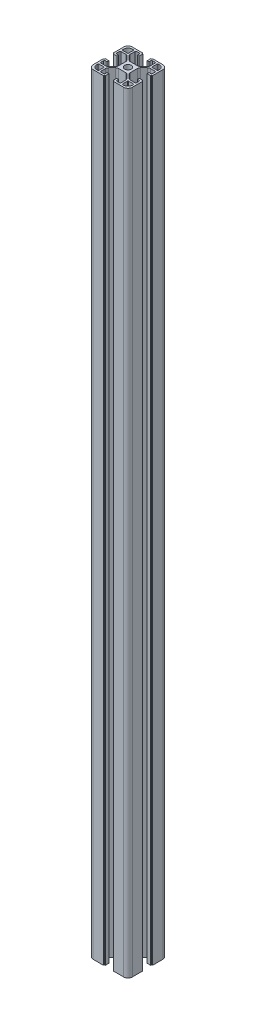
SolidWorks part; units mm, degrees
ref_plane "Front Plane" through (0, 0, 0) normal (0, 0, 1) x (1, 0, 0)
ref_plane "Top Plane" through (0, 0, 0) normal (0, 1, 0) x (1, 0, 0)
ref_plane "Right Plane" through (0, 0, 0) normal (1, 0, 0) x (0, 0, -1)
sketch "Sketch1" plane through (0, 0, 0) normal (0, 1, 0) x (1, 0, 0)
  line L0 (84.1702, 31.7204) -> (84.1702, 42.1204)
  line L1 (44.1702, 62.7204) -> (44.1702, 52.3204)
  line L2 (48.6702, 27.2204) -> (59.0702, 27.2204)
  line L3 (79.6702, 67.2204) -> (69.2702, 67.2204)
  line L4 (84.1702, 52.3204) -> (84.1702, 62.7204)
  line L6 (44.1702, 42.1204) -> (44.1702, 31.7204)
  line L7 (69.2702, 27.2204) -> (79.6702, 27.2204)
  line L10 (44.1702, 42.1204) -> (44.7702, 42.1204)
  line L11 (44.9702, 42.3204) -> (44.9702, 42.9204)
  line L12 (48.6702, 43.1204) -> (45.1702, 43.1204)
  line L13 (48.6702, 41.3204) -> (48.6702, 43.1204)
  line L14 (46.9702, 41.3204) -> (48.6702, 41.3204)
  line L15 (45.9702, 37.9704) -> (45.9702, 40.3204)
  line L16 (51.6169, 36.9704) -> (46.9702, 36.9704)
  line L17 (57.2915, 41.4024) -> (53.7382, 37.8491)
  line L18 (58.1702, 50.9171) -> (58.1702, 43.5237)
  line L19 (53.7382, 56.5917) -> (57.2915, 53.0384)
  line L20 (46.9702, 57.4704) -> (51.6169, 57.4704)
  line L21 (45.9702, 54.1204) -> (45.9702, 56.4704)
  line L22 (48.6702, 53.1204) -> (46.9702, 53.1204)
  line L23 (48.6702, 51.3204) -> (48.6702, 53.1204)
  line L24 (45.1702, 51.3204) -> (48.6702, 51.3204)
  line L25 (44.9702, 51.5204) -> (44.9702, 52.1204)
  line L26 (44.7702, 52.3204) -> (44.1702, 52.3204)
  line L28 (59.0702, 67.2204) -> (48.6702, 67.2204)
  line L29 (59.0702, 67.2204) -> (59.0702, 66.6204)
  line L30 (59.2702, 66.4204) -> (60.0702, 66.4204)
  line L31 (60.0702, 62.7204) -> (60.0702, 66.4204)
  line L32 (58.2702, 62.7204) -> (60.0702, 62.7204)
  line L33 (58.2702, 64.4204) -> (58.2702, 62.7204)
  line L34 (54.9202, 65.4204) -> (57.2702, 65.4204)
  line L35 (53.9202, 59.7737) -> (53.9202, 64.4204)
  line L36 (58.3522, 54.0991) -> (54.7989, 57.6524)
  line L37 (67.8669, 53.2204) -> (60.4735, 53.2204)
  line L38 (73.5415, 57.6524) -> (69.9882, 54.0991)
  line L39 (74.4202, 64.4204) -> (74.4202, 59.7737)
  line L40 (71.0702, 65.4204) -> (73.4202, 65.4204)
  line L41 (70.0702, 62.7204) -> (70.0702, 64.4204)
  line L42 (68.2702, 62.7204) -> (70.0702, 62.7204)
  line L43 (68.2702, 66.2204) -> (68.2702, 62.7204)
  line L44 (68.4702, 66.4204) -> (69.2702, 66.4204)
  line L45 (69.2702, 66.4204) -> (69.2702, 67.2204)
  line L48 (84.1702, 52.3204) -> (83.5702, 52.3204)
  line L49 (83.3702, 52.1204) -> (83.3702, 51.5204)
  line L50 (79.6702, 51.3204) -> (83.1702, 51.3204)
  line L51 (79.6702, 53.1204) -> (79.6702, 51.3204)
  line L52 (81.3702, 53.1204) -> (79.6702, 53.1204)
  line L53 (82.3702, 56.4704) -> (82.3702, 54.1204)
  line L54 (76.7235, 57.4704) -> (81.3702, 57.4704)
  line L55 (71.0489, 53.0384) -> (74.6022, 56.5917)
  line L56 (70.1702, 43.5237) -> (70.1702, 50.9171)
  line L57 (74.6022, 37.8491) -> (71.0489, 41.4024)
  line L58 (81.3702, 36.9704) -> (76.7235, 36.9704)
  line L59 (82.3702, 40.3204) -> (82.3702, 37.9704)
  line L60 (79.6702, 41.3204) -> (81.3702, 41.3204)
  line L61 (79.6702, 43.1204) -> (79.6702, 41.3204)
  line L62 (83.1702, 43.1204) -> (79.6702, 43.1204)
  line L63 (83.3702, 42.9204) -> (83.3702, 42.3204)
  line L64 (83.5702, 42.1204) -> (84.1702, 42.1204)
  line L67 (69.2702, 27.2204) -> (69.2702, 27.8204)
  line L68 (69.0702, 28.0204) -> (68.4702, 28.0204)
  line L69 (68.2702, 31.7204) -> (68.2702, 28.2204)
  line L70 (70.0702, 31.7204) -> (68.2702, 31.7204)
  line L71 (70.0702, 30.0204) -> (70.0702, 31.7204)
  line L72 (73.4202, 29.0204) -> (71.0702, 29.0204)
  line L73 (74.4202, 34.6671) -> (74.4202, 30.0204)
  line L74 (69.9882, 40.3417) -> (73.5415, 36.7884)
  line L75 (60.4735, 41.2204) -> (67.8669, 41.2204)
  line L76 (54.7989, 36.7884) -> (58.3522, 40.3417)
  line L77 (53.9202, 30.0204) -> (53.9202, 34.6671)
  line L78 (57.2702, 29.0204) -> (54.9202, 29.0204)
  line L79 (58.2702, 31.7204) -> (58.2702, 30.0204)
  line L80 (60.0702, 31.7204) -> (58.2702, 31.7204)
  line L81 (60.0702, 28.2204) -> (60.0702, 31.7204)
  line L82 (59.8702, 28.0204) -> (59.2702, 28.0204)
  line L83 (59.0702, 27.8204) -> (59.0702, 27.2204)
  line L84 (82.3702, 34.6704) -> (82.3702, 33.5204)
  line L85 (76.7202, 35.1704) -> (81.8702, 35.1704)
  line L86 (76.2202, 29.5204) -> (76.2202, 34.6704)
  line L87 (77.8702, 29.0204) -> (76.7202, 29.0204)
  line L88 (51.6202, 29.0204) -> (50.4702, 29.0204)
  line L89 (52.1202, 34.6704) -> (52.1202, 29.5204)
  line L90 (46.4702, 35.1704) -> (51.6202, 35.1704)
  line L91 (45.9702, 33.5204) -> (45.9702, 34.6704)
  line L92 (45.9702, 59.7704) -> (45.9702, 60.9204)
  line L93 (51.6202, 59.2704) -> (46.4702, 59.2704)
  line L94 (52.1202, 64.9204) -> (52.1202, 59.7704)
  line L95 (50.4702, 65.4204) -> (51.6202, 65.4204)
  line L96 (76.7202, 65.4204) -> (77.8702, 65.4204)
  line L97 (76.2202, 59.7704) -> (76.2202, 64.9204)
  line L98 (81.8702, 59.2704) -> (76.7202, 59.2704)
  line L99 (82.3702, 60.9204) -> (82.3702, 59.7704)
  arc A0 (60.7702, 47.2204) -> (67.5702, 47.2204) centre (64.1702, 47.2204) ccw
  arc A1 (44.1702, 31.7204) -> (48.6702, 27.2204) centre (48.6702, 31.7204) ccw
  arc A2 (44.7702, 42.1204) -> (44.9702, 42.3204) centre (44.7702, 42.3204) ccw
  arc A3 (45.1702, 43.1204) -> (44.9702, 42.9204) centre (45.1702, 42.9204) ccw
  arc A4 (46.9702, 41.3204) -> (45.9702, 40.3204) centre (46.9702, 40.3204) ccw
  arc A5 (45.9702, 37.9704) -> (46.9702, 36.9704) centre (46.9702, 37.9704) ccw
  arc A6 (51.6169, 36.9704) -> (53.7382, 37.8491) centre (51.6169, 39.9704) ccw
  arc A7 (57.2915, 41.4024) -> (58.1702, 43.5237) centre (55.1702, 43.5237) ccw
  arc A8 (58.1702, 50.9171) -> (57.2915, 53.0384) centre (55.1702, 50.9171) ccw
  arc A9 (53.7382, 56.5917) -> (51.6169, 57.4704) centre (51.6169, 54.4704) ccw
  arc A10 (46.9702, 57.4704) -> (45.9702, 56.4704) centre (46.9702, 56.4704) ccw
  arc A11 (45.9702, 54.1204) -> (46.9702, 53.1204) centre (46.9702, 54.1204) ccw
  arc A12 (44.9702, 51.5204) -> (45.1702, 51.3204) centre (45.1702, 51.5204) ccw
  arc A13 (44.9702, 52.1204) -> (44.7702, 52.3204) centre (44.7702, 52.1204) ccw
  arc A14 (48.6702, 67.2204) -> (44.1702, 62.7204) centre (48.6702, 62.7204) ccw
  arc A15 (59.0702, 66.6204) -> (59.2702, 66.4204) centre (59.2702, 66.6204) ccw
  arc A16 (58.2702, 64.4204) -> (57.2702, 65.4204) centre (57.2702, 64.4204) ccw
  arc A17 (54.9202, 65.4204) -> (53.9202, 64.4204) centre (54.9202, 64.4204) ccw
  arc A18 (53.9202, 59.7737) -> (54.7989, 57.6524) centre (56.9202, 59.7737) ccw
  arc A19 (58.3522, 54.0991) -> (60.4735, 53.2204) centre (60.4735, 56.2204) ccw
  arc A20 (67.8669, 53.2204) -> (69.9882, 54.0991) centre (67.8669, 56.2204) ccw
  arc A21 (73.5415, 57.6524) -> (74.4202, 59.7737) centre (71.4202, 59.7737) ccw
  arc A22 (74.4202, 64.4204) -> (73.4202, 65.4204) centre (73.4202, 64.4204) ccw
  arc A23 (71.0702, 65.4204) -> (70.0702, 64.4204) centre (71.0702, 64.4204) ccw
  arc A24 (68.4702, 66.4204) -> (68.2702, 66.2204) centre (68.4702, 66.2204) ccw
  arc A25 (84.1702, 62.7204) -> (79.6702, 67.2204) centre (79.6702, 62.7204) ccw
  arc A26 (83.5702, 52.3204) -> (83.3702, 52.1204) centre (83.5702, 52.1204) ccw
  arc A27 (83.1702, 51.3204) -> (83.3702, 51.5204) centre (83.1702, 51.5204) ccw
  arc A28 (81.3702, 53.1204) -> (82.3702, 54.1204) centre (81.3702, 54.1204) ccw
  arc A29 (82.3702, 56.4704) -> (81.3702, 57.4704) centre (81.3702, 56.4704) ccw
  arc A30 (76.7235, 57.4704) -> (74.6022, 56.5917) centre (76.7235, 54.4704) ccw
  arc A31 (71.0489, 53.0384) -> (70.1702, 50.9171) centre (73.1702, 50.9171) ccw
  arc A32 (70.1702, 43.5237) -> (71.0489, 41.4024) centre (73.1702, 43.5237) ccw
  arc A33 (74.6022, 37.8491) -> (76.7235, 36.9704) centre (76.7235, 39.9704) ccw
  arc A34 (81.3702, 36.9704) -> (82.3702, 37.9704) centre (81.3702, 37.9704) ccw
  arc A35 (82.3702, 40.3204) -> (81.3702, 41.3204) centre (81.3702, 40.3204) ccw
  arc A36 (83.3702, 42.9204) -> (83.1702, 43.1204) centre (83.1702, 42.9204) ccw
  arc A37 (83.3702, 42.3204) -> (83.5702, 42.1204) centre (83.5702, 42.3204) ccw
  arc A38 (79.6702, 27.2204) -> (84.1702, 31.7204) centre (79.6702, 31.7204) ccw
  arc A39 (69.2702, 27.8204) -> (69.0702, 28.0204) centre (69.0702, 27.8204) ccw
  arc A40 (68.2702, 28.2204) -> (68.4702, 28.0204) centre (68.4702, 28.2204) ccw
  arc A41 (70.0702, 30.0204) -> (71.0702, 29.0204) centre (71.0702, 30.0204) ccw
  arc A42 (73.4202, 29.0204) -> (74.4202, 30.0204) centre (73.4202, 30.0204) ccw
  arc A43 (74.4202, 34.6671) -> (73.5415, 36.7884) centre (71.4202, 34.6671) ccw
  arc A44 (69.9882, 40.3417) -> (67.8669, 41.2204) centre (67.8669, 38.2204) ccw
  arc A45 (60.4735, 41.2204) -> (58.3522, 40.3417) centre (60.4735, 38.2204) ccw
  arc A46 (54.7989, 36.7884) -> (53.9202, 34.6671) centre (56.9202, 34.6671) ccw
  arc A47 (53.9202, 30.0204) -> (54.9202, 29.0204) centre (54.9202, 30.0204) ccw
  arc A48 (57.2702, 29.0204) -> (58.2702, 30.0204) centre (57.2702, 30.0204) ccw
  arc A49 (59.8702, 28.0204) -> (60.0702, 28.2204) centre (59.8702, 28.2204) ccw
  arc A50 (59.2702, 28.0204) -> (59.0702, 27.8204) centre (59.2702, 27.8204) ccw
  arc A51 (82.3702, 34.6704) -> (81.8702, 35.1704) centre (81.8702, 34.6704) ccw
  arc A52 (76.7202, 35.1704) -> (76.2202, 34.6704) centre (76.7202, 34.6704) ccw
  arc A53 (76.2202, 29.5204) -> (76.7202, 29.0204) centre (76.7202, 29.5204) ccw
  arc A54 (77.8702, 29.0204) -> (82.3702, 33.5204) centre (77.8702, 33.5204) ccw
  arc A55 (51.6202, 29.0204) -> (52.1202, 29.5204) centre (51.6202, 29.5204) ccw
  arc A56 (52.1202, 34.6704) -> (51.6202, 35.1704) centre (51.6202, 34.6704) ccw
  arc A57 (46.4702, 35.1704) -> (45.9702, 34.6704) centre (46.4702, 34.6704) ccw
  arc A58 (45.9702, 33.5204) -> (50.4702, 29.0204) centre (50.4702, 33.5204) ccw
  arc A59 (45.9702, 59.7704) -> (46.4702, 59.2704) centre (46.4702, 59.7704) ccw
  arc A60 (51.6202, 59.2704) -> (52.1202, 59.7704) centre (51.6202, 59.7704) ccw
  arc A61 (52.1202, 64.9204) -> (51.6202, 65.4204) centre (51.6202, 64.9204) ccw
  arc A62 (50.4702, 65.4204) -> (45.9702, 60.9204) centre (50.4702, 60.9204) ccw
  arc A63 (76.7202, 65.4204) -> (76.2202, 64.9204) centre (76.7202, 64.9204) ccw
  arc A64 (76.2202, 59.7704) -> (76.7202, 59.2704) centre (76.7202, 59.7704) ccw
  arc A65 (81.8702, 59.2704) -> (82.3702, 59.7704) centre (81.8702, 59.7704) ccw
  arc A66 (82.3702, 60.9204) -> (77.8702, 65.4204) centre (77.8702, 60.9204) ccw
  arc A67 (67.5702, 47.2204) -> (60.7702, 47.2204) centre (64.1702, 47.2204) ccw
extrude "Boss-Extrude2" add sketch "Sketch1" along normal blind 786 from offset 0 separate body
